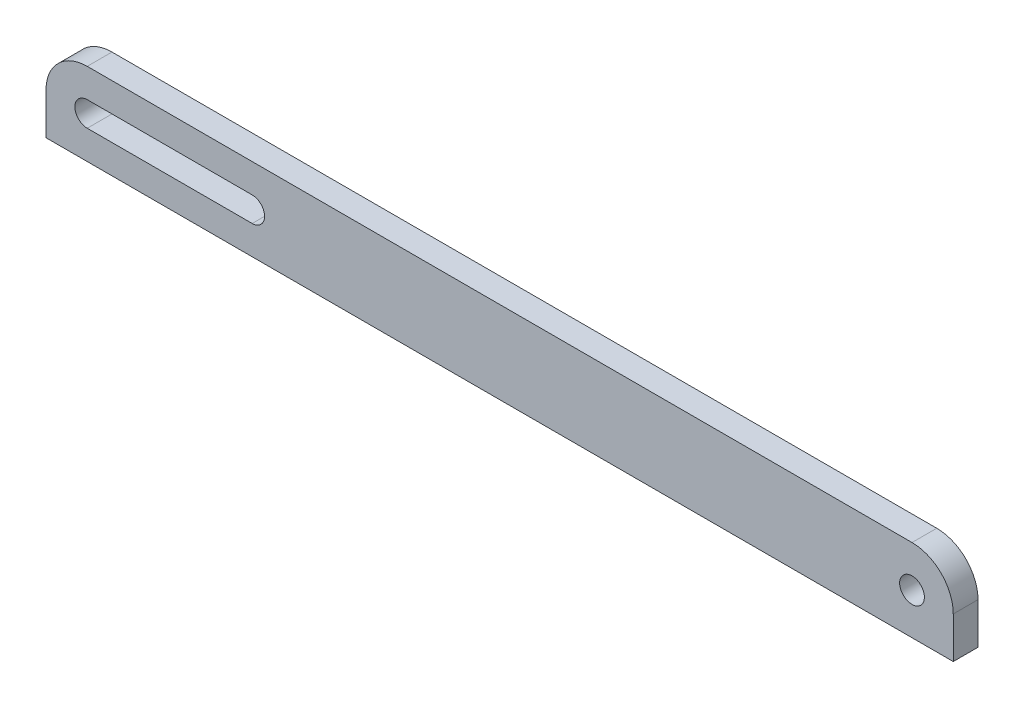
SolidWorks part; units mm, degrees
ref_plane "Front Plane" through (0, 0, 0) normal (0, 0, 1) x (1, 0, 0)
ref_plane "Top Plane" through (0, 0, 0) normal (0, 1, 0) x (1, 0, 0)
ref_plane "Right Plane" through (0, 0, 0) normal (1, 0, 0) x (0, 0, -1)
sketch "Sketch1" plane through (0, 0, 0) normal (0, 0, 1) x (1, 0, 0)
  line L0 (0, 5) -> (0, -5) construction
  line L1 (50, -5) -> (-50, -5)
  line L3 (50, 5) -> (-50, 5)
  line L4 (-50, -5) -> (-50, 5) construction
  line L5 (0, 0) -> (-50, 5) construction
  line L6 (0, 0) -> (-50, -5) construction
  line L7 (-55, 0) -> (-55, -5)
  line L8 (-55, -5) -> (-50, -5)
  line L9 (0, 0) -> (50, -5) construction
  line L10 (0, 0) -> (50, 5) construction
  line L11 (50, -5) -> (50, 5) construction
  line L12 (55, -5) -> (50, -5)
  line L13 (55, 0) -> (55, -5)
  line L14 (-50, 0) -> (-30, 0) construction
  line L15 (-50, 1.5) -> (-30, 1.5)
  line L16 (-50, -1.5) -> (-30, -1.5)
  arc A0 (-50, 5) -> (-55, 0) centre (-50, 0) ccw
  circle A1 centre (-50, 0) radius 1.5 construction
  circle A2 centre (50, 0) radius 1.5
  arc A3 (50, 5) -> (55, 0) centre (50, 0) cw
  arc A4 (-50, 1.5) -> (-50, -1.5) centre (-50, 0) ccw
  arc A5 (-30, -1.5) -> (-30, 1.5) centre (-30, 0) ccw
  point P0 (0, 0)
  point P17 (-40, 0)
  dimension "D3" = 3
  dimension "D1" = 50
  dimension "D2" = 10
  dimension "D4" = 20
extrude "Boss-Extrude1" add sketch "Sketch1" along normal blind 3
